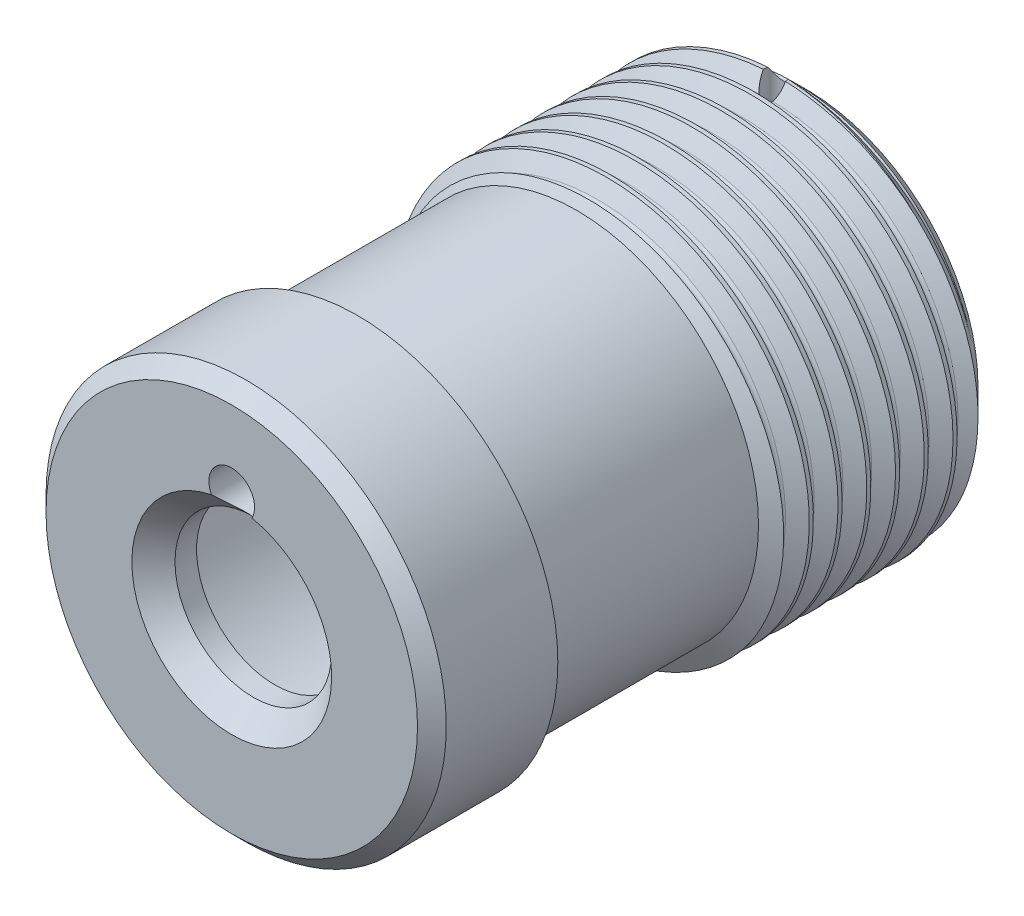
SolidWorks part; units mm, degrees
material "AISI 4130 Steel, normalized at 870C"
ref_plane "Front Plane" through (0, 0, 0) normal (0, 0, 1) x (1, 0, 0)
ref_plane "Top Plane" through (0, 0, 0) normal (0, 1, 0) x (1, 0, 0)
ref_plane "Right Plane" through (0, 0, 0) normal (1, 0, 0) x (0, 0, -1)
sketch "Sketch1" plane through (0, 0, 0) normal (1, 0, 0) x (0, 0, -1)
  line L0 (-46.2567, 0) -> (176.137, 0) construction
  line L1 (0, 19.3) -> (0, 27.85)
  line L3 (80, 25.3) -> (80, 22.15)
  line L6 (0, 27.85) -> (80, 27.85)
  line L7 (80, 27.85) -> (80, 25.3)
  line L8 (6, 17.15) -> (6, 10.9)
  line L9 (6, 10.9) -> (0, 10.9)
  line L10 (0, 10.9) -> (0, 19.3)
  line L12 (11, 22.15) -> (80, 22.15)
  arc A0 (11, 22.15) -> (6, 17.15) centre (11, 17.15) ccw
  dimension "D2" = 5
  dimension "D3" = 80
  dimension "D5" = 55.7
  dimension "D6" = 21.8
  dimension "D8" = 6
  dimension "D11" = 5.7
  dimension "D14" = 44.3
revolve "Revolve1" add sketch "Sketch1" angle 360 about L0
chamfer "Chamfer1" distance 4 angle 45 1 edges at (27.85, 0, -80)
sketch "Sketch2" plane through (0, 0, -80) normal (0, 0, -1) x (-1, 0, 0)
  circle A0 centre (0, 0) radius 28
curve "Helix/Spiral1" pitch 4 height 34.4 turns 8.6
sketch "Sketch3" plane through (0, 0, 0) normal (1, 0, 0) x (0, 0, -1)
  line L0 (83.6021, 28) -> (82.3011, 25.7465)
  line L1 (81.3011, 25.7465) -> (80, 28)
  line L2 (81.8011, 24.8804) -> (81.8011, 29.4651) construction
  line L3 (80, 28) -> (79.7113, 28.5)
  line L4 (79.7113, 28.5) -> (83.8908, 28.5)
  line L5 (83.8908, 28.5) -> (83.6021, 28)
  line L6 (81.3011, 25.7465) -> (82.3011, 25.7465) construction
  line L7 (80, 28) -> (83.6021, 28) construction
  line L8 (0, 0) -> (95.4072, 0) construction
  line L9 (80.8011, 26.6125) -> (82.8011, 26.6125) construction
  arc A0 (81.3011, 25.7465) -> (82.3011, 25.7465) centre (81.8011, 26.0351) ccw
  spline S1 degree 3 poles (80, 28) (79.9431, 28) (79.8288, 27.3214) (79.6577, 24.3408) (79.4866, 19.6117) (79.3154, 13.4737) (79.1443, 6.3678) (78.9731, -1.1956) (78.802, -8.673) (78.6308, -15.5274) (78.4597, -21.2664) (78.2886, -25.4777) (78.1174, -27.8587) (77.9463, -28.2384) (77.7751, -26.5896) (77.604, -23.0307) (77.4328, -17.8173) (77.2617, -11.324) (77.0905, -4.0172) (76.9194, 3.5782) (76.7483, 10.9166) (76.5771, 17.4707) (76.406, 22.7698) (76.2348, 26.4331) (76.0637, 28.1976) (75.8925, 27.9365) (75.7214, 25.6685) (75.5502, 21.5566) (75.3791, 15.8961) (75.208, 9.0936) (75.0368, 1.638) (74.8657, -5.9354) (74.6945, -13.0824) (74.5234, -19.2895) (74.3522, -24.111) (74.1811, -27.2004) (74.01, -28.3358) (73.8388, -27.4357) (73.6677, -24.5647) (73.4965, -19.929) (73.3254, -13.8617) (73.1542, -6.7986) (72.9831, 0.7529) (72.8119, 8.2503) (72.6408, 15.155) (72.4697, 20.9711) (72.2985, 25.2806) (72.1274, 27.7741) (71.9562, 28.2723) (71.7851, 26.7396) (71.6139, 23.286) (71.4428, 18.1595) (71.2716, 11.7286) (71.1005, 4.4551) (70.9294, -3.1384) (70.7582, -10.5065) (70.5871, -17.1198) (70.4159, -22.5033) (70.2448, -26.2702) (70.0736, -28.15) (69.9025, -28.0075) (69.7313, -25.8531) (69.5602, -21.8415) (69.3891, -16.2608) (69.2179, -9.512) (69.0468, -2.0799) (68.8756, 5.5016) (68.7045, 12.6879) (68.5333, 18.9627) (68.3622, 23.8753) (68.191, 27.0728) (68.0199, 28.3255) (67.8488, 27.5433) (67.6776, 24.7825) (67.5065, 20.2415) (67.3353, 14.2463) (67.1642, 7.2277) (66.993, -0.3101) (66.8219, -7.8256) (66.6507, -14.7789) (66.4796, -20.6706) (66.3085, -25.0774) (66.1373, -27.6826) (65.9662, -28.2993) (65.795, -26.883) (65.6239, -23.5355) (65.4527, -18.4974) (65.2816, -12.1304) (65.1104, -4.892) (64.9393, 2.6978) (64.7682, 10.0938) (64.597, 16.7647) (64.4259, 22.2313) (64.2547, 26.1009) (64.0836, 28.0954) (63.9124, 28.0717) (63.7413, 26.0313) (63.5701, 22.121) (63.399, 16.6216) (63.2279, 9.9281) (63.0567, 2.5214) (62.8856, -5.0664) (62.7144, -12.2903) (62.5433, -18.6312) (62.3721, -23.6338) (62.201, -26.9386) (62.0299, -28.3082) (61.8587, -27.6442) (61.6876, -24.9943) (61.5164, -20.549) (61.3453, -14.6274) (61.1741, -7.6551) (61.003, -0.1329) (60.8318, 7.3989) (60.6607, 14.3992) (60.4896, 20.3651) (60.3184, 24.868) (60.1473, 27.5845) (59.9761, 28.3194) (59.805, 27.0199) (59.6338, 23.7794) (59.4627, 18.8307) (59.2915, 12.5292) (59.1204, 5.3277) (58.9493, -2.2566) (58.7781, -9.6787) (58.607, -16.4056) (58.4358, -21.9539) (58.2647, -25.9251) (58.0935, -28.034) (57.9224, -28.129) (57.7512, -26.2032) (57.5801, -22.3952) (57.409, -16.9783) (57.2378, -10.3417) (57.0667, -2.9623) (56.8955, 4.63) (56.7244, 11.8897) (56.5532, 18.2952) (56.3821, 23.3865) (56.2109, 26.7977) (56.0398, 28.2839) (55.8687, 27.7383) (55.6975, 25.2) (55.5264, 20.8515) (55.3552, 15.005) (55.1841, 8.0806) (55.0129, 0.5758) (54.8418, -6.9704) (54.6706, -14.0159) (54.4995, -20.0546) (54.3284, -24.6525) (54.1572, -27.4796) (53.9861, -28.3325) (53.8149, -27.1502) (53.6438, -24.0174) (53.4726, -19.1594) (53.3015, -12.9249) (53.1303, -5.762) (52.9592, 1.8148) (52.7881, 9.2613) (52.6169, 16.0424) (52.4458, 21.6712) (52.2746, 25.7431) (52.1035, 27.9657) (51.9323, 28.1794) (51.7612, 26.3687) (51.59, 22.6638) (51.4189, 17.3308) (51.2478, 10.7528) (51.0766, 3.4024) (50.9055, -4.1925) (50.7343, -11.4862) (50.5632, -17.9547) (50.392, -23.1335) (50.2209, -26.6504) (50.0498, -28.2528) (49.8786, -27.8256) (49.7075, -25.3996) (49.5363, -21.1489) (49.3652, -15.3789) (49.194, -8.5042) (49.0229, -1.0185) (48.8517, 6.5403) (48.6806, 13.6293) (48.5095, 19.7392) (48.3383, 24.4311) (48.1672, 27.3679) (47.996, 28.3387) (47.8249, 27.2738) (47.6537, 24.2496) (47.4826, 19.4834) (47.3114, 13.3175) (47.1403, 6.195) (46.9692, -1.3726) (46.798, -8.8415) (46.6269, -15.6753) (46.4557, -21.3831) (46.2846, -25.5547) (46.1134, -27.8908) (45.9423, -28.2224) (45.7712, -26.5298) (45.6569, -24.1229) (45.6, -22.6525) knots 0 0 0 0 0.004975 0.00995 0.014925 0.0199 0.024876 0.029851 0.034826 0.039801 0.044776 0.049751 0.054726 0.059701 0.064677 0.069652 0.074627 0.079602 0.084577 0.089552 0.094527 0.099502 0.104478 0.109453 0.114428 0.119403 0.124378 0.129353 0.134328 0.139303 0.144279 0.149254 0.154229 0.159204 0.164179 0.169154 0.174129 0.179104 0.18408 0.189055 0.19403 0.199005 0.20398 0.208955 0.21393 0.218905 0.223881 0.228856 0.233831 0.238806 0.243781 0.248756 0.253731 0.258706 0.263682 0.268657 0.273632 0.278607 0.283582 0.288557 0.293532 0.298507 0.303483 0.308458 0.313433 0.318408 0.323383 0.328358 0.333333 0.338308 0.343284 0.348259 0.353234 0.358209 0.363184 0.368159 0.373134 0.378109 0.383085 0.38806 0.393035 0.39801 0.402985 0.40796 0.412935 0.41791 0.422886 0.427861 0.432836 0.437811 0.442786 0.447761 0.452736 0.457711 0.462687 0.467662 0.472637 0.477612 0.482587 0.487562 0.492537 0.497512 0.502488 0.507463 0.512438 0.517413 0.522388 0.527363 0.532338 0.537313 0.542289 0.547264 0.552239 0.557214 0.562189 0.567164 0.572139 0.577114 0.58209 0.587065 0.59204 0.597015 0.60199 0.606965 0.61194 0.616915 0.621891 0.626866 0.631841 0.636816 0.641791 0.646766 0.651741 0.656716 0.661692 0.666667 0.671642 0.676617 0.681592 0.686567 0.691542 0.696517 0.701493 0.706468 0.711443 0.716418 0.721393 0.726368 0.731343 0.736318 0.741294 0.746269 0.751244 0.756219 0.761194 0.766169 0.771144 0.776119 0.781095 0.78607 0.791045 0.79602 0.800995 0.80597 0.810945 0.81592 0.820896 0.825871 0.830846 0.835821 0.840796 0.845771 0.850746 0.855721 0.860697 0.865672 0.870647 0.875622 0.880597 0.885572 0.890547 0.895522 0.900498 0.905473 0.910448 0.915423 0.920398 0.925373 0.930348 0.935323 0.940299 0.945274 0.950249 0.955224 0.960199 0.965174 0.970149 0.975124 0.9801 0.985075 0.99005 0.995025 1 1 1 1 construction
  dimension "D1" = 30
  dimension "D2" = 30
  dimension "D3" = 1
  dimension "D4" = 2
  dimension "D5" = 26.6125
  dimension "D6" = 0.5
sweep "Cut-Sweep1" cut profiles "Sketch3" path "Helix/Spiral1"
chamfer "Chamfer2" distance 2 angle 45 1 edges at (27.85, 0, 0)
sketch "Sketch4" plane through (0, 0, 0) normal (0, 1, 0) x (1, 0, 0)
  line L0 (22.15, 80) -> (-22.15, 80) construction
  circle A0 centre (0, 75.5) radius 1.5
  dimension "D1" = 3
  dimension "D2" = 4.5
extrude "Cut-Extrude1" cut sketch "Sketch4" against normal through all and the other way through all
sketch "Sketch5" plane through (0, 0, 0) normal (1, 0, 0) x (0, 0, -1)
  line L0 (0, 0) -> (92.3768, 0) construction
  line L1 (48, 25.3) -> (19, 25.3)
  line L2 (19, 25.3) -> (14.6603, 32.8166)
  line L3 (14.6603, 32.8166) -> (52.3397, 32.8166)
  line L4 (52.3397, 32.8166) -> (48, 25.3)
  line L6 (80, -23.85) -> (80, 23.85) construction
  dimension "D1" = 60
  dimension "D2" = 29
  dimension "D3" = 32
  dimension "D4" = 60
  dimension "D5" = 50.6
revolve "Cut-Revolve1" cut sketch "Sketch5" angle 360 about L0
chamfer "Chamfer3" distance 3 angle 45 1 edges at (10.9, 0, 0)
sketch "Sketch6" plane through (0, 0, 0) normal (0, 0, 1) x (1, 0, 0)
  line L0 (0, 10.9) -> (31.5175, 10.9) construction
  line L1 (0, 11.9) -> (31.5175, 11.9) construction
  circle A0 centre (0, 15.075) radius 3.175
  circle A1 centre (0, 0) radius 10.9 construction
  dimension "D1" = 6.35
  dimension "D2" = 1
  dimension "D3" = 15.075
extrude "Cut-Extrude2" cut sketch "Sketch6" against normal through all
